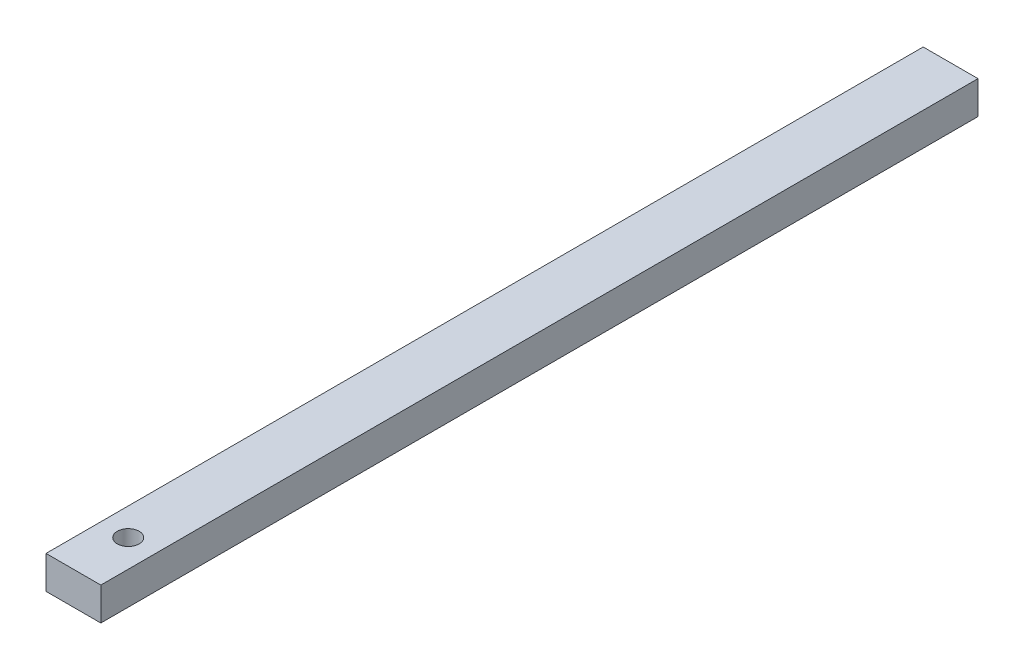
SolidWorks part; units mm, degrees
material "ABS"
ref_plane "Front Plane" through (0, 0, 0) normal (0, 0, 1) x (1, 0, 0)
ref_plane "Top Plane" through (0, 0, 0) normal (0, 1, 0) x (1, 0, 0)
ref_plane "Right Plane" through (0, 0, 0) normal (1, 0, 0) x (0, 0, -1)
sketch "Sketch1" plane through (0, 0, 0) normal (0, 0, 1) x (1, 0, 0)
  line L1 (2.5, -1.5) -> (-2.5, -1.5)
  line L2 (2.5, -1.5) -> (2.5, 1.5)
  line L3 (2.5, 1.5) -> (-2.5, 1.5)
  line L4 (-2.5, -1.5) -> (-2.5, 1.5)
  line L5 (2.5, -1.5) -> (-2.5, 1.5) construction
  line L6 (2.5, 1.5) -> (-2.5, -1.5) construction
  point P0 (0, 0)
  dimension "D1" = 3
  dimension "D2" = 5
extrude "Boss-Extrude1" add sketch "Sketch1" along normal blind 80
sketch "Sketch2" plane through (0, 1.5, 0) normal (0, 1, 0) x (1, 0, 0)
  line L0 (2.5, -80) -> (-2.5, -80) construction
  circle A0 centre (0, -75) radius 1
  dimension "D2" = 2
  dimension "D1" = 5
extrude "Cut-Extrude1" cut sketch "Sketch2" against normal through all
sketch "Sketch3" plane through (0, 1.5, 0) normal (0, 1, 0) x (1, 0, 0)
  circle A0 centre (0, -5) radius 1
  circle A1 centre (0, -39) radius 1
  dimension "D1" = 2
  dimension "D2" = 2
  dimension "D3" = 34
  dimension "D4" = 5
